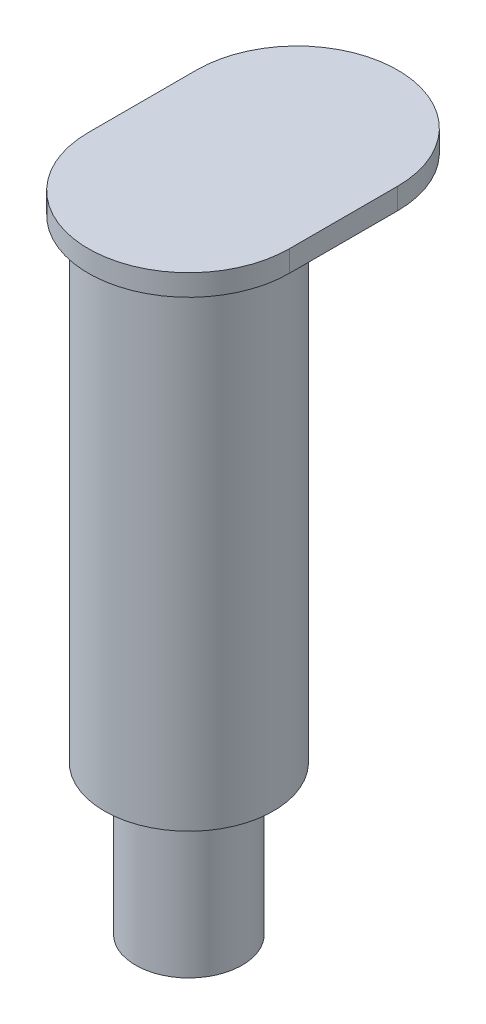
SolidWorks part; units mm, degrees
ref_plane "Front Plane" through (0, 0, 0) normal (0, 0, 1) x (1, 0, 0)
ref_plane "Top Plane" through (0, 0, 0) normal (0, 1, 0) x (1, 0, 0)
ref_plane "Right Plane" through (0, 0, 0) normal (1, 0, 0) x (0, 0, -1)
sketch "Sketch1" plane through (0, 0, 0) normal (0, 1, 0) x (1, 0, 0)
  circle A0 centre (0, 0) radius 15.875
  dimension "D1" = 31.75
extrude "Boss-Extrude1" add sketch "Sketch1" along normal blind 88.9
sketch "Sketch2" plane through (0, 88.9, 0) normal (0, 1, 0) x (1, 0, 0)
  line L0 (0, 0) -> (0, 20.32) construction
  line L1 (-18.875, 0) -> (-18.875, 20.32)
  line L2 (18.875, 0) -> (18.875, 20.32)
  line L3 (0, -18.875) -> (0, 39.195) construction
  arc A0 (-18.875, 0) -> (18.875, 0) centre (0, 0) ccw
  arc A1 (18.875, 20.32) -> (-18.875, 20.32) centre (0, 20.32) ccw
  circle A2 centre (0, 0) radius 15.875 construction
  point P3 (0, 10.16)
  dimension "D1" = 3
  dimension "D2" = 20.32
extrude "Boss-Extrude2" add sketch "Sketch2" along normal blind 4
sketch "Sketch3" plane through (0, 0, 0) normal (0, -1, 0) x (1, 0, 0)
  circle A0 centre (0, 0) radius 10
  dimension "D1" = 20
extrude "Boss-Extrude3" add sketch "Sketch3" along normal blind 28
